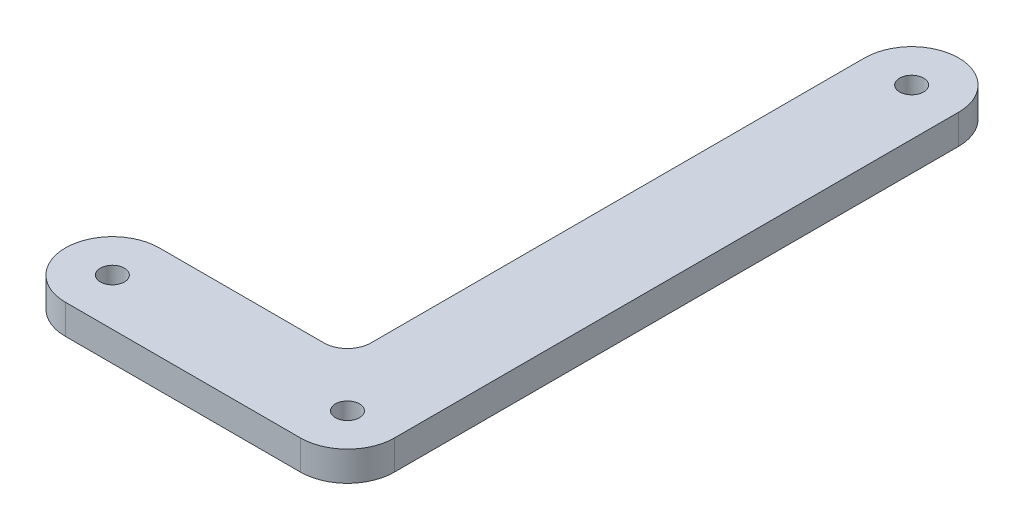
SolidWorks part; units mm, degrees
ref_plane "Front Plane" through (0, 0, 0) normal (0, 0, 1) x (1, 0, 0)
ref_plane "Top Plane" through (0, 0, 0) normal (0, 1, 0) x (1, 0, 0)
ref_plane "Right Plane" through (0, 0, 0) normal (1, 0, 0) x (0, 0, -1)
sketch "Sketch1" plane through (0, 0, 0) normal (0, 1, 0) x (1, 0, 0)
  line L1 (-18.6184, -6.35) -> (13.1316, -6.35)
  line L3 (-18.6184, 6.35) -> (3.6066, 6.35)
  line L6 (19.4816, 0) -> (19.4816, 76.2)
  line L8 (6.7816, 9.525) -> (6.7816, 76.2)
  arc A0 (13.1316, -6.35) -> (19.4816, 0) centre (13.1316, 0) ccw
  arc A1 (-18.6184, 6.35) -> (-18.6184, -6.35) centre (-18.6184, 0) ccw
  circle A2 centre (-18.6184, 0) radius 1.625
  circle A3 centre (13.1316, 0) radius 1.625
  arc A4 (3.6066, 6.35) -> (6.7816, 9.525) centre (3.6066, 9.525) ccw
  arc A5 (19.4816, 76.2) -> (6.7816, 76.2) centre (13.1316, 76.2) ccw
  circle A6 centre (13.1316, 76.2) radius 1.625
  point P0 (0, 0)
  dimension "D3" = 3.25
  dimension "D4" = 3.25
  dimension "D2" = 3.175
  dimension "D7" = 3.25
  dimension "D1" = 12.7
  dimension "D5" = 12.7
  dimension "D6" = 76.2
extrude "Boss-Extrude1" add sketch "Sketch1" along normal blind 4
